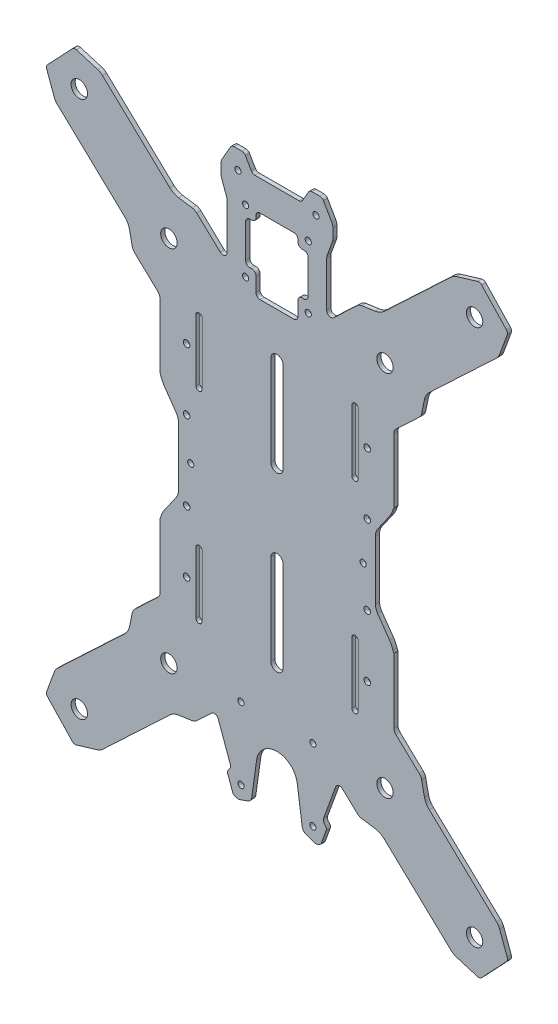
SolidWorks part; units mm, degrees
ref_plane "Front Plane" through (0, 0, 0) normal (0, 0, 1) x (1, 0, 0)
ref_plane "Top Plane" through (0, 0, 0) normal (0, 1, 0) x (1, 0, 0)
ref_plane "Right Plane" through (0, 0, 0) normal (1, 0, 0) x (0, 0, -1)
sketch "Model" plane through (0, 0, 0) normal (0, 0, 1) x (1, 0, 0)
  line L0 (200.4127, 281.3131) -> (207.0194, 282.2803)
  line L1 (211.3501, 284.3765) -> (244.1291, 315.2966)
  line L2 (246.5156, 316.677) -> (256.8221, 319.7815)
  line L3 (270.8811, 306.4885) -> (258.8538, 319.2389)
  line L4 (271.3043, 304.4286) -> (267.604, 294.3207)
  line L5 (266.0868, 292.0187) -> (233.3078, 261.0987)
  line L6 (230.9627, 256.8976) -> (229.6119, 250.3586)
  line L7 (228.4393, 248.258) -> (217.0717, 237.5351)
  line L8 (216.1302, 211.086) -> (216.1302, 235.3528)
  line L9 (219.1302, 210.086) -> (217.1302, 210.086)
  line L10 (220.1302, 206.9971) -> (220.1302, 209.086)
  line L11 (213.96, 199.2031) -> (208.2153, 190.9987)
  line L12 (207.1302, 158.6884) -> (207.1302, 187.5573)
  line L13 (208.2153, 155.2469) -> (213.96, 147.0426)
  line L14 (220.1302, 137.1597) -> (220.1302, 139.2486)
  line L15 (217.1302, 136.1597) -> (219.1302, 136.1597)
  line L16 (216.1302, 110.8929) -> (216.1302, 135.1597)
  line L17 (217.0717, 108.7106) -> (228.4393, 97.9876)
  line L18 (229.6119, 95.8871) -> (230.9627, 89.3481)
  line L19 (233.3078, 85.147) -> (266.0868, 54.2269)
  line L20 (267.604, 51.9249) -> (271.3043, 41.817)
  line L21 (258.8538, 27.0068) -> (270.8811, 39.7571)
  line L22 (256.8221, 26.4641) -> (246.5156, 29.5687)
  line L23 (244.1291, 30.9491) -> (211.3501, 61.8692)
  line L24 (207.0194, 63.9653) -> (200.4127, 64.9325)
  line L25 (198.2474, 65.9806) -> (191.0122, 72.8055)
  line L26 (181.8313, 55.7445) -> (187.7604, 72.0347)
  line L27 (182.1786, 53.7749) -> (182.7352, 53.1115)
  line L28 (183.0825, 51.1419) -> (180.7129, 44.6315)
  line L29 (179.1809, 43.3459) -> (177.8615, 43.1133)
  line L30 (177.3458, 43.1584) -> (173.3678, 44.6063)
  line L31 (171.423, 47.0078) -> (169.0329, 64.0146)
  line L32 (149.2275, 64.0146) -> (146.8374, 47.0078)
  line L33 (144.8926, 44.6063) -> (140.9146, 43.1584)
  line L34 (139.0795, 43.3459) -> (140.3989, 43.1133)
  line L35 (135.1779, 51.1419) -> (137.5474, 44.6315)
  line L36 (136.0818, 53.7749) -> (135.5252, 53.1115)
  line L37 (130.5, 72.0347) -> (136.4291, 55.7445)
  line L38 (120.013, 65.9806) -> (127.2482, 72.8055)
  line L39 (111.241, 63.9653) -> (117.8476, 64.9325)
  line L40 (74.1313, 30.9491) -> (106.9103, 61.8692)
  line L41 (61.4383, 26.4641) -> (71.7448, 29.5687)
  line L42 (47.3793, 39.7571) -> (59.4066, 27.0068)
  line L43 (50.6563, 51.9249) -> (46.9561, 41.817)
  line L44 (84.9526, 85.147) -> (52.1736, 54.2269)
  line L45 (88.6485, 95.8871) -> (87.2977, 89.3481)
  line L46 (101.1887, 108.7106) -> (89.8211, 97.9876)
  line L47 (102.1302, 135.1597) -> (102.1302, 110.8929)
  line L48 (99.1302, 136.1597) -> (101.1302, 136.1597)
  line L49 (98.1302, 139.2486) -> (98.1302, 137.1597)
  line L50 (110.0451, 155.2469) -> (104.3004, 147.0426)
  line L51 (111.1302, 187.5573) -> (111.1302, 158.6884)
  line L52 (104.3004, 199.2031) -> (110.0451, 190.9987)
  line L53 (98.1302, 209.086) -> (98.1302, 206.9971)
  line L54 (101.1302, 210.086) -> (99.1302, 210.086)
  line L55 (102.1302, 235.3528) -> (102.1302, 211.086)
  line L56 (89.8211, 248.258) -> (101.1887, 237.5351)
  line L57 (87.2977, 256.8976) -> (88.6485, 250.3586)
  line L58 (52.1736, 292.0187) -> (84.9526, 261.0987)
  line L59 (46.9561, 304.4286) -> (50.6563, 294.3207)
  line L60 (59.4066, 319.2389) -> (47.3793, 306.4885)
  line L61 (71.7448, 316.677) -> (61.4383, 319.7815)
  line L62 (106.9103, 284.3765) -> (74.1313, 315.2966)
  line L63 (117.8476, 281.3131) -> (111.241, 282.2803)
  line L64 (131.5078, 269.4221) -> (120.013, 280.2651)
  line L65 (134.8802, 292.8447) -> (134.8802, 270.877)
  line L66 (132.1214, 301.1297) -> (134.639, 294.2128)
  line L67 (131.8802, 307.2589) -> (131.8802, 302.4977)
  line L68 (136.499, 316.3307) -> (132.4161, 309.2589)
  line L69 (142.0293, 317.3307) -> (138.231, 317.3307)
  line L70 (146.6481, 311.3307) -> (143.7614, 316.3307)
  line L71 (169.8802, 310.3307) -> (148.3802, 310.3307)
  line L72 (171.6122, 311.3307) -> (174.499, 316.3307)
  line L73 (176.231, 317.3307) -> (180.0293, 317.3307)
  line L74 (181.7614, 316.3307) -> (185.8443, 309.2589)
  line L75 (186.3802, 307.2589) -> (186.3802, 302.4977)
  line L76 (186.139, 301.1297) -> (183.6214, 294.2128)
  line L77 (183.3802, 292.8447) -> (183.3802, 270.877)
  line L78 (186.7526, 269.4221) -> (198.2474, 280.2651)
  line L79 (119.6302, 109.1228) -> (119.6302, 139.1228)
  line L80 (122.6302, 139.1228) -> (122.6302, 109.1228)
  line L81 (198.6302, 237.1228) -> (198.6302, 207.1228)
  line L82 (195.6302, 207.1228) -> (195.6302, 237.1228)
  line L83 (146.8802, 270.1228) -> (145.8802, 270.1228)
  line L84 (148.8802, 261.1228) -> (148.8802, 268.1228)
  line L85 (167.3802, 259.1228) -> (150.8802, 259.1228)
  line L86 (169.3802, 268.1228) -> (169.3802, 261.1228)
  line L87 (172.3802, 270.1228) -> (171.3802, 270.1228)
  line L88 (174.3802, 288.6228) -> (174.3802, 272.1228)
  line L89 (171.3802, 290.6228) -> (172.3802, 290.6228)
  line L90 (169.3802, 293.6228) -> (169.3802, 292.6228)
  line L91 (150.8802, 295.6228) -> (167.3802, 295.6228)
  line L92 (148.8802, 292.6228) -> (148.8802, 293.6228)
  line L93 (145.8802, 290.6228) -> (146.8802, 290.6228)
  line L94 (143.8802, 272.1228) -> (143.8802, 288.6228)
  line L95 (162.1302, 237.1228) -> (162.1302, 193.1228)
  line L96 (156.1302, 193.1228) -> (156.1302, 237.1228)
  line L97 (156.1302, 109.1228) -> (156.1302, 153.1228)
  line L98 (162.1302, 153.1228) -> (162.1302, 109.1228)
  line L99 (122.6302, 237.1228) -> (122.6302, 207.1228)
  line L100 (119.6302, 207.1228) -> (119.6302, 237.1228)
  line L101 (195.6302, 109.1228) -> (195.6302, 139.1228)
  line L102 (198.6302, 139.1228) -> (198.6302, 109.1228)
  arc A0 (200.4127, 281.3131) -> (198.2474, 280.2651) centre (200.9921, 277.3553) ccw
  arc A1 (207.0194, 282.2803) -> (211.3501, 284.3765) centre (205.8606, 290.1959) ccw
  arc A2 (246.5156, 316.677) -> (244.1291, 315.2966) centre (248.2461, 310.932) ccw
  arc A3 (258.8538, 319.2389) -> (256.8221, 319.7815) centre (257.399, 317.8665) ccw
  arc A4 (271.3043, 304.4286) -> (270.8811, 306.4885) centre (269.4262, 305.1162) ccw
  arc A5 (266.0868, 292.0187) -> (267.604, 294.3207) centre (261.9697, 296.3833) ccw
  arc A6 (233.3078, 261.0987) -> (230.9627, 256.8976) centre (238.7973, 255.2792) ccw
  arc A7 (228.4393, 248.258) -> (229.6119, 250.3586) centre (225.6946, 251.1678) ccw
  arc A8 (217.0717, 237.5351) -> (216.1302, 235.3528) centre (219.1302, 235.3528) ccw
  arc A9 (216.1302, 211.086) -> (217.1302, 210.086) centre (217.1302, 211.086) ccw
  arc A10 (220.1302, 209.086) -> (219.1302, 210.086) centre (219.1302, 209.086) ccw
  arc A11 (219.3067, 206.0128) -> (220.1302, 206.9971) centre (219.1302, 206.9971) ccw
  arc A12 (219.3067, 206.0128) -> (215.6502, 202.726) centre (220.1302, 201.4193) ccw
  arc A13 (213.96, 199.2031) -> (215.6502, 202.726) centre (204.1302, 206.086) ccw
  arc A14 (208.2153, 190.9987) -> (207.1302, 187.5573) centre (213.1302, 187.5573) ccw
  arc A15 (207.1302, 158.6884) -> (208.2153, 155.2469) centre (213.1302, 158.6884) ccw
  arc A16 (215.6502, 143.5197) -> (213.96, 147.0426) centre (204.1302, 140.1597) ccw
  arc A17 (215.6502, 143.5197) -> (219.3067, 140.2329) centre (220.1302, 144.8263) ccw
  arc A18 (220.1302, 139.2486) -> (219.3067, 140.2329) centre (219.1302, 139.2486) ccw
  arc A19 (219.1302, 136.1597) -> (220.1302, 137.1597) centre (219.1302, 137.1597) ccw
  arc A20 (217.1302, 136.1597) -> (216.1302, 135.1597) centre (217.1302, 135.1597) ccw
  arc A21 (216.1302, 110.8929) -> (217.0717, 108.7106) centre (219.1302, 110.8929) ccw
  arc A22 (229.6119, 95.8871) -> (228.4393, 97.9876) centre (225.6946, 95.0779) ccw
  arc A23 (230.9627, 89.3481) -> (233.3078, 85.147) centre (238.7973, 90.9665) ccw
  arc A24 (267.604, 51.9249) -> (266.0868, 54.2269) centre (261.9697, 49.8623) ccw
  arc A25 (270.8811, 39.7571) -> (271.3043, 41.817) centre (269.4262, 41.1295) ccw
  arc A26 (256.8221, 26.4641) -> (258.8538, 27.0068) centre (257.399, 28.3791) ccw
  arc A27 (244.1291, 30.9491) -> (246.5156, 29.5687) centre (248.2461, 35.3137) ccw
  arc A28 (211.3501, 61.8692) -> (207.0194, 63.9653) centre (205.8606, 56.0497) ccw
  arc A29 (198.2474, 65.9806) -> (200.4127, 64.9325) centre (200.9921, 68.8903) ccw
  arc A30 (191.0122, 72.8055) -> (187.7604, 72.0347) centre (189.6398, 71.3507) ccw
  arc A31 (181.8313, 55.7445) -> (182.1786, 53.7749) centre (183.7106, 55.0605) ccw
  arc A32 (183.0825, 51.1419) -> (182.7352, 53.1115) centre (181.2031, 51.8259) ccw
  arc A33 (179.1809, 43.3459) -> (180.7129, 44.6315) centre (178.8336, 45.3155) ccw
  arc A34 (177.3458, 43.1584) -> (177.8615, 43.1133) centre (177.6878, 44.0981) ccw
  arc A35 (171.423, 47.0078) -> (173.3678, 44.6063) centre (174.3938, 47.4253) ccw
  arc A36 (169.0329, 64.0146) -> (149.2275, 64.0146) centre (159.1302, 62.6228) ccw
  arc A37 (144.8926, 44.6063) -> (146.8374, 47.0078) centre (143.8666, 47.4253) ccw
  arc A38 (140.3989, 43.1133) -> (140.9146, 43.1584) centre (140.5726, 44.0981) ccw
  arc A39 (137.5474, 44.6315) -> (139.0795, 43.3459) centre (139.4268, 45.3155) ccw
  arc A40 (135.5252, 53.1115) -> (135.1779, 51.1419) centre (137.0572, 51.8259) ccw
  arc A41 (136.0818, 53.7749) -> (136.4291, 55.7445) centre (134.5497, 55.0605) ccw
  arc A42 (130.5, 72.0347) -> (127.2482, 72.8055) centre (128.6206, 71.3507) ccw
  arc A43 (117.8476, 64.9325) -> (120.013, 65.9806) centre (117.2683, 68.8903) ccw
  arc A44 (111.241, 63.9653) -> (106.9103, 61.8692) centre (112.3997, 56.0497) ccw
  arc A45 (71.7448, 29.5687) -> (74.1313, 30.9491) centre (70.0143, 35.3137) ccw
  arc A46 (59.4066, 27.0068) -> (61.4383, 26.4641) centre (60.8614, 28.3791) ccw
  arc A47 (46.9561, 41.817) -> (47.3793, 39.7571) centre (48.8342, 41.1295) ccw
  arc A48 (52.1736, 54.2269) -> (50.6563, 51.9249) centre (56.2907, 49.8623) ccw
  arc A49 (84.9526, 85.147) -> (87.2977, 89.3481) centre (79.4631, 90.9665) ccw
  arc A50 (89.8211, 97.9876) -> (88.6485, 95.8871) centre (92.5658, 95.0779) ccw
  arc A51 (101.1887, 108.7106) -> (102.1302, 110.8929) centre (99.1302, 110.8929) ccw
  arc A52 (102.1302, 135.1597) -> (101.1302, 136.1597) centre (101.1302, 135.1597) ccw
  arc A53 (98.1302, 137.1597) -> (99.1302, 136.1597) centre (99.1302, 137.1597) ccw
  arc A54 (98.9537, 140.2329) -> (98.1302, 139.2486) centre (99.1302, 139.2486) ccw
  arc A55 (98.9537, 140.2329) -> (102.6102, 143.5197) centre (98.1302, 144.8263) ccw
  arc A56 (104.3004, 147.0426) -> (102.6102, 143.5197) centre (114.1302, 140.1597) ccw
  arc A57 (110.0451, 155.2469) -> (111.1302, 158.6884) centre (105.1302, 158.6884) ccw
  arc A58 (111.1302, 187.5573) -> (110.0451, 190.9987) centre (105.1302, 187.5573) ccw
  arc A59 (102.6102, 202.726) -> (104.3004, 199.2031) centre (114.1302, 206.086) ccw
  arc A60 (102.6102, 202.726) -> (98.9537, 206.0128) centre (98.1302, 201.4193) ccw
  arc A61 (98.1302, 206.9971) -> (98.9537, 206.0128) centre (99.1302, 206.9971) ccw
  arc A62 (99.1302, 210.086) -> (98.1302, 209.086) centre (99.1302, 209.086) ccw
  arc A63 (101.1302, 210.086) -> (102.1302, 211.086) centre (101.1302, 211.086) ccw
  arc A64 (102.1302, 235.3528) -> (101.1887, 237.5351) centre (99.1302, 235.3528) ccw
  arc A65 (88.6485, 250.3586) -> (89.8211, 248.258) centre (92.5658, 251.1678) ccw
  arc A66 (87.2977, 256.8976) -> (84.9526, 261.0987) centre (79.4631, 255.2792) ccw
  arc A67 (50.6563, 294.3207) -> (52.1736, 292.0187) centre (56.2907, 296.3833) ccw
  arc A68 (47.3793, 306.4885) -> (46.9561, 304.4286) centre (48.8342, 305.1162) ccw
  arc A69 (61.4383, 319.7815) -> (59.4066, 319.2389) centre (60.8614, 317.8665) ccw
  arc A70 (74.1313, 315.2966) -> (71.7448, 316.677) centre (70.0143, 310.932) ccw
  arc A71 (106.9103, 284.3765) -> (111.241, 282.2803) centre (112.3997, 290.1959) ccw
  arc A72 (120.013, 280.2651) -> (117.8476, 281.3131) centre (117.2683, 277.3553) ccw
  arc A73 (131.5078, 269.4221) -> (134.8802, 270.877) centre (132.8802, 270.8769) ccw
  arc A74 (134.8802, 292.8447) -> (134.639, 294.2128) centre (130.8802, 292.8447) ccw
  arc A75 (131.8802, 302.4977) -> (132.1214, 301.1297) centre (135.8802, 302.4977) ccw
  arc A76 (132.4161, 309.2589) -> (131.8802, 307.2589) centre (135.8802, 307.2589) ccw
  arc A77 (138.231, 317.3307) -> (136.499, 316.3307) centre (138.231, 315.3307) ccw
  arc A78 (143.7614, 316.3307) -> (142.0293, 317.3307) centre (142.0293, 315.3307) ccw
  arc A79 (146.6481, 311.3307) -> (148.3802, 310.3307) centre (148.3802, 312.3307) ccw
  arc A80 (169.8802, 310.3307) -> (171.6122, 311.3307) centre (169.8802, 312.3307) ccw
  arc A81 (176.231, 317.3307) -> (174.499, 316.3307) centre (176.231, 315.3307) ccw
  arc A82 (181.7614, 316.3307) -> (180.0293, 317.3307) centre (180.0293, 315.3307) ccw
  arc A83 (186.3802, 307.2589) -> (185.8443, 309.2589) centre (182.3802, 307.2589) ccw
  arc A84 (186.139, 301.1297) -> (186.3802, 302.4977) centre (182.3802, 302.4977) ccw
  arc A85 (183.6214, 294.2128) -> (183.3802, 292.8447) centre (187.3802, 292.8447) ccw
  arc A86 (183.3802, 270.877) -> (186.7526, 269.4221) centre (185.3802, 270.8769) ccw
  arc A87 (122.6302, 139.1228) -> (119.6302, 139.1228) centre (121.1302, 139.1228) ccw
  arc A88 (119.6302, 109.1228) -> (122.6302, 109.1228) centre (121.1302, 109.1228) ccw
  arc A89 (195.6302, 207.1228) -> (198.6302, 207.1228) centre (197.1302, 207.1228) ccw
  arc A90 (198.6302, 237.1228) -> (195.6302, 237.1228) centre (197.1302, 237.1228) ccw
  arc A91 (143.8802, 272.1228) -> (145.8802, 270.1228) centre (145.8802, 272.1228) ccw
  arc A92 (148.8802, 268.1228) -> (146.8802, 270.1228) centre (146.8802, 268.1228) ccw
  arc A93 (148.8802, 261.1228) -> (150.8802, 259.1228) centre (150.8802, 261.1228) ccw
  arc A94 (167.3802, 259.1228) -> (169.3802, 261.1228) centre (167.3802, 261.1228) ccw
  arc A95 (171.3802, 270.1228) -> (169.3802, 268.1228) centre (171.3802, 268.1228) ccw
  arc A96 (172.3802, 270.1228) -> (174.3802, 272.1228) centre (172.3802, 272.1228) ccw
  arc A97 (174.3802, 288.6228) -> (172.3802, 290.6228) centre (172.3802, 288.6228) ccw
  arc A98 (169.3802, 292.6228) -> (171.3802, 290.6228) centre (171.3802, 292.6228) ccw
  arc A99 (169.3802, 293.6228) -> (167.3802, 295.6228) centre (167.3802, 293.6228) ccw
  arc A100 (150.8802, 295.6228) -> (148.8802, 293.6228) centre (150.8802, 293.6228) ccw
  arc A101 (146.8802, 290.6228) -> (148.8802, 292.6228) centre (146.8802, 292.6228) ccw
  arc A102 (145.8802, 290.6228) -> (143.8802, 288.6228) centre (145.8802, 288.6228) ccw
  circle A103 centre (174.3802, 265.1228) radius 1.5
  circle A104 centre (143.8802, 295.6228) radius 1.5
  circle A105 centre (176.6302, 84.7678) radius 1.5
  arc A106 (156.1302, 193.1228) -> (162.1302, 193.1228) centre (159.1302, 193.1228) ccw
  arc A107 (162.1302, 237.1228) -> (156.1302, 237.1228) centre (159.1302, 237.1228) ccw
  circle A108 centre (141.6302, 49.7678) radius 1.5
  circle A109 centre (106.4955, 262.7726) radius 4
  circle A110 centre (62.8496, 303.9434) radius 4
  circle A111 centre (106.4955, 83.4731) radius 4
  circle A112 centre (62.8496, 42.3023) radius 4
  circle A113 centre (255.4108, 42.3023) radius 4
  circle A114 centre (211.7649, 83.4731) radius 4
  circle A115 centre (255.4108, 303.9434) radius 4
  circle A116 centre (211.7649, 262.7726) radius 4
  circle A117 centre (176.6302, 49.7678) radius 1.5
  arc A118 (162.1302, 153.1228) -> (156.1302, 153.1228) centre (159.1302, 153.1228) ccw
  arc A119 (156.1302, 109.1228) -> (162.1302, 109.1228) centre (159.1302, 109.1228) ccw
  circle A120 centre (141.6302, 84.7678) radius 1.5
  circle A121 centre (174.3802, 295.6228) radius 1.5
  circle A122 centre (143.8802, 265.1228) radius 1.5
  circle A123 centre (140.1302, 308.3307) radius 3.5 construction
  circle A124 centre (178.1302, 308.3307) radius 3.5 construction
  circle A125 centre (117.1302, 173.1228) radius 3.5 construction
  circle A126 centre (201.1302, 173.1228) radius 3.5 construction
  arc A127 (119.6302, 207.1228) -> (122.6302, 207.1228) centre (121.1302, 207.1228) ccw
  arc A128 (122.6302, 237.1228) -> (119.6302, 237.1228) centre (121.1302, 237.1228) ccw
  arc A129 (198.6302, 139.1228) -> (195.6302, 139.1228) centre (197.1302, 139.1228) ccw
  arc A130 (195.6302, 109.1228) -> (198.6302, 109.1228) centre (197.1302, 109.1228) ccw
  circle A131 centre (201.1302, 173.1228) radius 1.5
  circle A132 centre (117.1302, 173.1228) radius 1.5
  circle A133 centre (178.1302, 308.3307) radius 1.5
  circle A134 centre (140.1302, 308.3307) radius 1.5
extrude "Boss-Extrude1" add sketch "Model" along normal blind 2
sketch "Sketch1" plane through (0, 0, 2) normal (0, 0, 1) x (1, 0, 0)
  line L0 (216.1302, 211.086) -> (216.1302, 235.3528) construction
  line L1 (216.1302, 214.7223) -> (221.5771, 214.7223)
  line L2 (216.1302, 214.7223) -> (216.1302, 133.6837)
  line L3 (216.1302, 133.6837) -> (221.5771, 133.6837)
  line L4 (221.5771, 214.7223) -> (221.5771, 133.6837)
  line L5 (102.1302, 235.3528) -> (102.1302, 211.086) construction
  line L6 (102.1302, 214.7223) -> (95.9029, 214.7223)
  line L7 (102.1302, 214.7223) -> (102.1302, 133.6837)
  line L8 (102.1302, 133.6837) -> (95.9029, 133.6837)
  line L9 (95.9029, 214.7223) -> (95.9029, 133.6837)
extrude "Cut-Extrude1" cut sketch "Sketch1" against normal up to next
sketch "Sketch3" plane through (0, 0, -25) normal (0, 0, 1) x (1, 0, 0)
  circle A0 centre (115.1302, 124.1503) radius 1.6 construction
  circle A1 centre (203.1302, 124.1502) radius 1.6 construction
  circle A2 centre (115.1302, 154.1503) radius 1.6 construction
  circle A3 centre (203.1302, 154.1502) radius 1.6 construction
  circle A4 centre (203.1302, 192.6503) radius 1.6 construction
  circle A5 centre (115.1302, 192.6503) radius 1.6 construction
  circle A6 centre (115.1302, 222.6503) radius 1.6 construction
  circle A7 centre (203.1302, 222.6503) radius 1.6 construction
  circle A8 centre (115.1302, 124.1503) radius 1.6
  circle A9 centre (203.1302, 124.1502) radius 1.6
  circle A10 centre (115.1302, 154.1503) radius 1.6
  circle A11 centre (203.1302, 154.1502) radius 1.6
  circle A12 centre (203.1302, 192.6503) radius 1.6
  circle A13 centre (115.1302, 192.6503) radius 1.6
  circle A14 centre (115.1302, 222.6503) radius 1.6
  circle A15 centre (203.1302, 222.6503) radius 1.6
sketch "Sketch4" plane through (0, 0, 0) normal (0, 0, -1) x (-1, 0, 0)
  circle A0 centre (-203.1302, 124.1502) radius 1.6 construction
  circle A1 centre (-203.1302, 154.1502) radius 1.6 construction
  circle A2 centre (-203.1302, 192.6503) radius 1.6 construction
  circle A3 centre (-203.1302, 222.6503) radius 1.6 construction
  circle A4 centre (-115.1302, 222.6503) radius 1.6 construction
  circle A5 centre (-115.1302, 192.6503) radius 1.6 construction
  circle A6 centre (-115.1302, 154.1503) radius 1.6 construction
  circle A7 centre (-115.1302, 124.1503) radius 1.6 construction
  circle A8 centre (-203.1302, 124.1502) radius 1.6
  circle A9 centre (-203.1302, 154.1502) radius 1.6
  circle A10 centre (-203.1302, 192.6503) radius 1.6
  circle A11 centre (-203.1302, 222.6503) radius 1.6
  circle A12 centre (-115.1302, 222.6503) radius 1.6
  circle A13 centre (-115.1302, 192.6503) radius 1.6
  circle A14 centre (-115.1302, 154.1503) radius 1.6
  circle A15 centre (-115.1302, 124.1503) radius 1.6
extrude "Cut-Extrude2" cut sketch "Sketch4" against normal up to next
